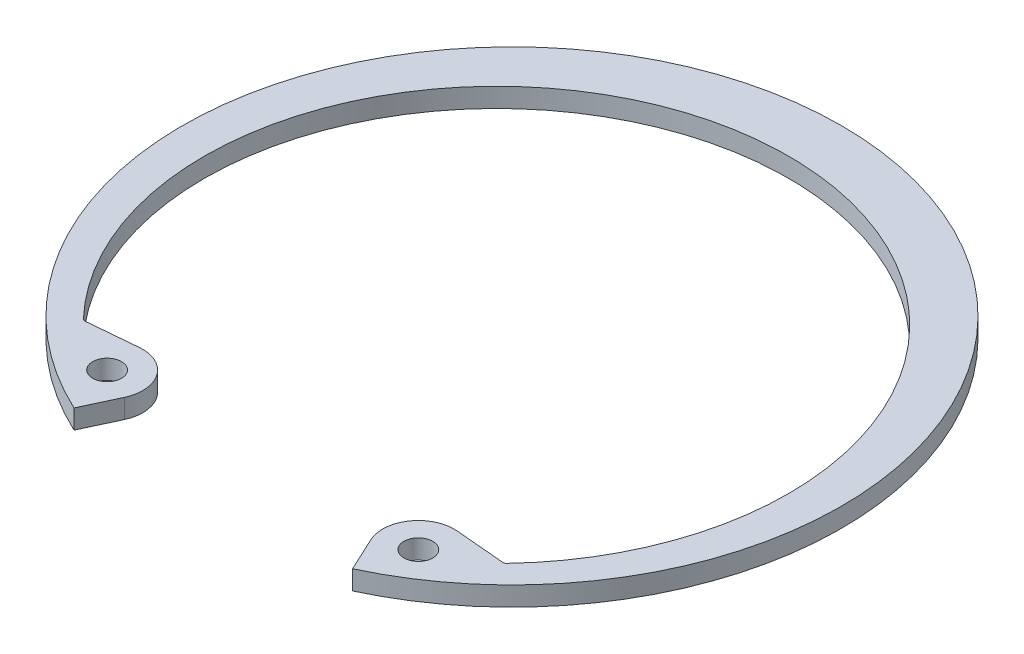
SolidWorks part; units mm, degrees
material "Cast Carbon Steel"
ref_plane "Front" through (0, 0, 0) normal (0, 0, 1) x (1, 0, 0)
ref_plane "Top" through (0, 0, 0) normal (0, 1, 0) x (1, 0, 0)
ref_plane "Right" through (0, 0, 0) normal (1, 0, 0) x (0, 0, -1)
sketch "Sketch2" plane through (0, 0, 0) normal (0, 1, 0) x (1, 0, 0)
  line L0 (0, 0) -> (0, -26.9494) construction
  line L1 (-17.2119, -17.8414) -> (-18.7109, -19.3952) construction
  line L2 (11.3893, -24.4245) -> (10.0795, -21.6156)
  line L3 (-11.3893, -24.4245) -> (-10.0795, -21.6156)
  line L4 (0, 22.6314) -> (0, 26.9494) construction
  line L5 (17.2119, -17.8414) -> (12.9814, -17.4713)
  line L6 (-17.2119, -17.8414) -> (-12.9814, -17.4713)
  line L7 (11.1797, -17.9035) -> (-0.4364, -25.1571) construction
  line L8 (-0.4364, -25.1571) -> (2.6579, -30.1124) construction
  line L9 (2.6579, -30.1124) -> (14.274, -22.8588) construction
  line L10 (11.1797, -17.9035) -> (14.274, -22.8588) construction
  line L11 (12.7269, -20.3811) -> (10.0795, -21.6156) construction
  line L12 (12.7269, -20.3811) -> (14.274, -22.8588) construction
  line L13 (11.1797, -17.9035) -> (-11.1797, -17.9035) construction
  line L14 (-11.1797, -17.9035) -> (-14.274, -22.8588) construction
  line L15 (-26.9494, 0) -> (26.9494, 0) construction
  arc A1 (11.3893, -24.4245) -> (-11.3893, -24.4245) centre (0, 0) ccw
  arc A2 (17.2119, -17.8414) -> (-17.2119, -17.8414) centre (0, -1.2648) ccw
  circle A3 centre (0, 0) radius 26.9494 construction
  arc A4 (10.0795, -21.6156) -> (12.9814, -17.4713) centre (12.7269, -20.3811) cw
  arc A5 (-10.0795, -21.6156) -> (-12.9814, -17.4713) centre (-12.7269, -20.3811) ccw
  circle A6 centre (12.7269, -20.3811) radius 1.1811
  circle A7 centre (-12.7269, -20.3811) radius 1.1811
  arc A8 (17.2119, -17.8414) -> (-17.2119, -17.8414) centre (0, -1.2648) cw construction
  circle A9 centre (0, 0) radius 20.066 construction
  point P5 (12.7269, -20.3811)
  point P10 (11.1797, -17.9035)
  dimension "D1" = 60
  dimension "D2" = 60
  dimension "L" = 40.132
  dimension "R" = 2.3622
  dimension "Df" = 53.8988
  dimension "H" = 5.842
  dimension "Angle" = 25
  dimension "Sec. Max" = 4.318
  dimension "Sec. Min" = 2.159
extrude "Extrude1" add sketch "Sketch2" against normal blind 1.5748
fillet "Fillet1" radius 0.254 2 edges at (-17.2119, -0.7874, 17.8414) (17.2119, -0.7874, 17.8414)
sketch "Sketch3" plane through (0, 0, 0) normal (1, 0, 0) x (0, 0, -1)
  line L0 (-25.4, -16.4592) -> (-25.4, -1.651)
  line L1 (-25.4, -1.651) -> (-26.9494, -1.651)
  line L2 (-26.9494, -1.651) -> (-26.9494, 0.0762)
  line L3 (-26.9494, 0.0762) -> (-25.4, 0.0762)
  line L4 (-25.4, 0.0762) -> (-25.4, 2.4384)
  line L5 (-25.4, -16.4592) -> (-28.4988, -16.4592)
  line L6 (-25.4, -1.651) -> (0, -1.651) construction
  line L7 (-25.4, 2.4384) -> (-28.4988, 2.4384)
  line L8 (0, 130.3401) -> (0, 164.6301) construction
  line L9 (0, -1.651) -> (0, 0.0762) construction
  line L10 (0, 0.0762) -> (-25.4, 0.0762) construction
  line L11 (-26.9494, -0.7874) -> (0, -0.7874) construction
  line L12 (0, -135.0899) -> (0, 130.3401) construction
  line L13 (-17.753, -1.5748) -> (22.6314, -1.5748) construction
  line L14 (-28.4988, -16.4592) -> (-28.4988, 2.4384)
  dimension "D1" = 0.7874
  dimension "Shaft Lg" = 18.8976
  dimension "Dg" = 53.8988
  dimension "Db" = 50.8
  dimension "W" = 1.7272
  dimension "D2" = 1.5494
  dimension "D3" = 2.3622
  dimension "D4" = 1.5494
revolve "Revolve1" [suppressed] add sketch "Sketch3" angle 360 about L8
delete or keep bodies "Body-Delete1" [suppressed] type delete bodies bodies 116
equation "\"D3@Sketch3\" = \"Shaft Lg@Sketch3\"/8"
equation "\"Shaft Lg@Sketch3\" = \"D1@Extrude1\"*12"
equation "\"D1@Sketch3\" = \"D1@Extrude1\"/2"
equation "\"D2@Sketch3\" = \"D4@Sketch3\""
